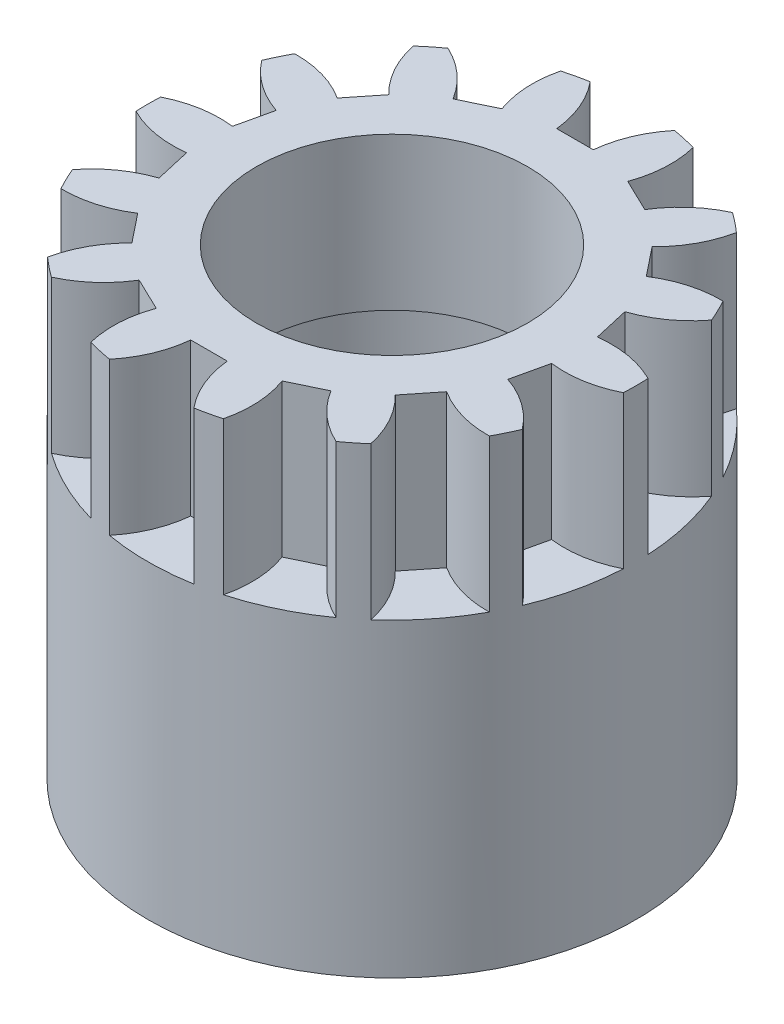
SolidWorks part; units mm, degrees
material "ABS"
ref_plane "Front Plane" through (0, 0, 0) normal (0, 0, 1) x (1, 0, 0)
ref_plane "Top Plane" through (0, 0, 0) normal (0, 1, 0) x (1, 0, 0)
ref_plane "Right Plane" through (0, 0, 0) normal (1, 0, 0) x (0, 0, -1)
sketch "Sketch3" plane through (0, 0, 0) normal (0, 1, 0) x (1, 0, 0)
  circle A2 centre (0, 0) radius 8
  dimension "D1" = 16
extrude "Boss-Extrude3" add sketch "Sketch3" along normal blind 5
sketch "Sketch4" plane through (0, 5, 0) normal (0, 1, 0) x (1, 0, 0)
  line L0 (-0.6, 6) -> (0.6, 6)
  line L1 (0, 0) -> (0, 6) construction
  line L2 (0, 6) -> (0, 8) construction
  line L3 (0, 0) -> (-0.6, 6) construction
  line L4 (0, 0) -> (0.6, 6) construction
  line L5 (2.0627, 5.6661) -> (3.1439, 5.1455)
  line L6 (4.3169, 4.21) -> (5.0651, 3.2718)
  line L7 (5.7161, 1.9201) -> (5.9831, 0.7502)
  line L8 (5.9831, -0.7502) -> (5.7161, -1.9201)
  line L9 (5.0651, -3.2718) -> (4.3169, -4.21)
  line L10 (3.1439, -5.1455) -> (2.0627, -5.6661)
  line L11 (0.6, -6) -> (-0.6, -6)
  line L12 (-2.0627, -5.6661) -> (-3.1439, -5.1455)
  line L13 (-4.3169, -4.21) -> (-5.0651, -3.2718)
  line L14 (-5.7161, -1.9201) -> (-5.9831, -0.7502)
  line L15 (-5.9831, 0.7502) -> (-5.7161, 1.9201)
  line L16 (-5.0651, 3.2718) -> (-4.3169, 4.21)
  line L17 (-3.1439, 5.1455) -> (-2.0627, 5.6661)
  arc A0 (-1.3832, 7.8795) -> (-0.6, 6) centre (-4.0826, 5.6517) cw
  circle A1 centre (0, 0) radius 8 construction
  arc A2 (0.6, 6) -> (1.3832, 7.8795) centre (4.0826, 5.6517) cw
  arc A4 (-1.3832, 7.8795) -> (1.3832, 7.8795) centre (0, 0) cw
  arc A5 (2.1726, 7.6993) -> (2.0627, 5.6661) centre (-1.2261, 6.8634) cw
  arc A6 (2.1726, 7.6993) -> (4.665, 6.4991) centre (0, 0) cw
  arc A7 (3.1439, 5.1455) -> (4.665, 6.4991) centre (6.1305, 3.3207) cw
  arc A8 (5.2981, 5.9942) -> (4.3169, 4.21) centre (1.8732, 6.7157) cw
  arc A9 (5.2981, 5.9942) -> (7.0229, 3.8314) centre (0, 0) cw
  arc A10 (5.0651, 3.2718) -> (7.0229, 3.8314) centre (6.9642, 0.3319) cw
  arc A11 (7.3742, 3.1019) -> (5.7161, 1.9201) centre (4.6016, 5.2379) cw
  arc A12 (7.3742, 3.1019) -> (7.9897, 0.4049) centre (0, 0) cw
  arc A13 (5.9831, 0.7502) -> (7.9897, 0.4049) centre (6.4185, -2.7226) cw
  arc A14 (7.9897, -0.4049) -> (5.9831, -0.7502) centre (6.4185, 2.7226) cw
  arc A15 (7.9897, -0.4049) -> (7.3742, -3.1019) centre (0, 0) cw
  arc A16 (5.7161, -1.9201) -> (7.3742, -3.1019) centre (4.6016, -5.2379) cw
  arc A17 (7.0229, -3.8314) -> (5.0651, -3.2718) centre (6.9642, -0.3319) cw
  arc A18 (7.0229, -3.8314) -> (5.2981, -5.9942) centre (0, 0) cw
  arc A19 (4.3169, -4.21) -> (5.2981, -5.9942) centre (1.8732, -6.7157) cw
  arc A20 (4.665, -6.4991) -> (3.1439, -5.1455) centre (6.1305, -3.3207) cw
  arc A21 (4.665, -6.4991) -> (2.1726, -7.6993) centre (0, 0) cw
  arc A22 (2.0627, -5.6661) -> (2.1726, -7.6993) centre (-1.2261, -6.8634) cw
  arc A23 (1.3832, -7.8795) -> (0.6, -6) centre (4.0826, -5.6517) cw
  arc A24 (1.3832, -7.8795) -> (-1.3832, -7.8795) centre (0, 0) cw
  arc A25 (-0.6, -6) -> (-1.3832, -7.8795) centre (-4.0826, -5.6517) cw
  arc A26 (-2.1726, -7.6993) -> (-2.0627, -5.6661) centre (1.2261, -6.8634) cw
  arc A27 (-2.1726, -7.6993) -> (-4.665, -6.4991) centre (0, 0) cw
  arc A28 (-3.1439, -5.1455) -> (-4.665, -6.4991) centre (-6.1305, -3.3207) cw
  arc A29 (-5.2981, -5.9942) -> (-4.3169, -4.21) centre (-1.8732, -6.7157) cw
  arc A30 (-5.2981, -5.9942) -> (-7.0229, -3.8314) centre (0, 0) cw
  arc A31 (-5.0651, -3.2718) -> (-7.0229, -3.8314) centre (-6.9642, -0.3319) cw
  arc A32 (-7.3742, -3.1019) -> (-5.7161, -1.9201) centre (-4.6016, -5.2379) cw
  arc A33 (-7.3742, -3.1019) -> (-7.9897, -0.4049) centre (0, 0) cw
  arc A34 (-5.9831, -0.7502) -> (-7.9897, -0.4049) centre (-6.4185, 2.7226) cw
  arc A35 (-7.9897, 0.4049) -> (-5.9831, 0.7502) centre (-6.4185, -2.7226) cw
  arc A36 (-7.9897, 0.4049) -> (-7.3742, 3.1019) centre (0, 0) cw
  arc A37 (-5.7161, 1.9201) -> (-7.3742, 3.1019) centre (-4.6016, 5.2379) cw
  arc A38 (-7.0229, 3.8314) -> (-5.0651, 3.2718) centre (-6.9642, 0.3319) cw
  arc A39 (-7.0229, 3.8314) -> (-5.2981, 5.9942) centre (0, 0) cw
  arc A40 (-4.3169, 4.21) -> (-5.2981, 5.9942) centre (-1.8732, 6.7157) cw
  arc A41 (-4.665, 6.4991) -> (-3.1439, 5.1455) centre (-6.1305, 3.3207) cw
  arc A42 (-4.665, 6.4991) -> (-2.1726, 7.6993) centre (0, 0) cw
  arc A43 (-2.0627, 5.6661) -> (-2.1726, 7.6993) centre (1.2261, 6.8634) cw
  point P70 (0, 0)
  point P96 (0, 0)
  dimension "D2" = 3.5
  dimension "D1" = 2
  dimension "D3" = 1.2
  dimension "D4" = 14
extrude "Cut-Extrude1" cut sketch "Sketch4" against normal up to surface (5 mm away) up to face at (0, 0, 8)
sketch "Sketch6" plane through (0, 5, 0) normal (0, 1, 0) x (1, 0, 0)
  circle A0 centre (0, 0) radius 4.445
  dimension "D1" = 8.89
extrude "Cut-Extrude2" cut sketch "Sketch6" against normal through all
sketch "Sketch7" plane through (0, 5, 0) normal (0, 1, 0) x (1, 0, 0)
  circle A0 centre (0, 0) radius 7
  dimension "D1" = 14
sketch "Sketch8" plane through (0, 0, 0) normal (0, -1, 0) x (1, 0, 0)
  circle A0 centre (0, 0) radius 8
  circle A1 centre (0, 0) radius 5.08
  dimension "D1" = 10.16
extrude "Boss-Extrude4" add sketch "Sketch8" along normal blind 10.16
